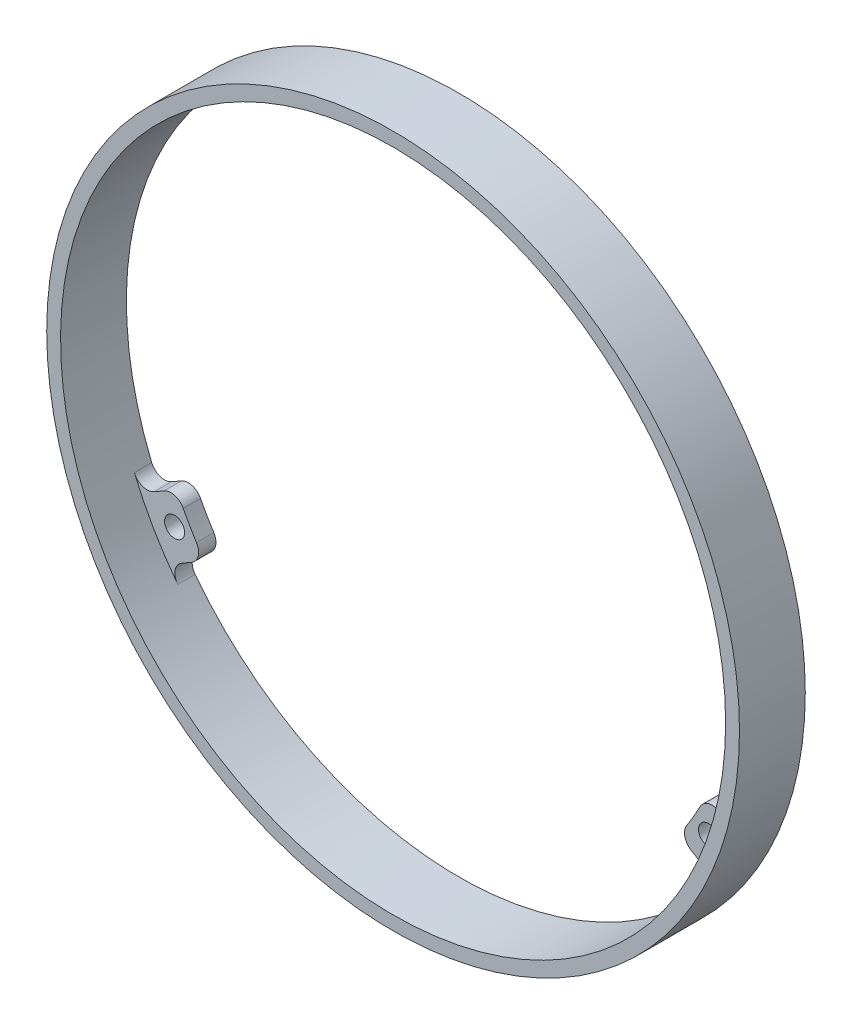
SolidWorks part; units mm, degrees
material "ABS"
ref_plane "Front Plane" through (0, 0, 0) normal (0, 0, 1) x (1, 0, 0)
ref_plane "Top Plane" through (0, 0, 0) normal (0, 1, 0) x (1, 0, 0)
ref_plane "Right Plane" through (0, 0, 0) normal (1, 0, 0) x (0, 0, -1)
sketch "Sketch1" plane through (0, 0, 0) normal (0, 0, 1) x (1, 0, 0)
  circle A0 centre (0, 0) radius 50
  circle A1 centre (0, 0) radius 48
  dimension "D1" = 100
  dimension "D2" = 2
extrude "Extrude1" add sketch "Sketch1" along normal blind 9.5
sketch "Sketch2" plane through (0, 0, 0) normal (0, 0, 1) x (1, 0, 0)
  line L0 (-4, 47.833) -> (-4, 41.8091)
  line L1 (0, 0) -> (0, 48) construction
  line L2 (4, 47.833) -> (4, 41.8091)
  arc A0 (4, 47.833) -> (-4, 47.833) centre (0, 0) ccw
  arc A1 (4, 41.8091) -> (-4, 41.8091) centre (0, 0) ccw
  circle A2 centre (0, 0) radius 48 construction
  dimension "D1" = 6
  dimension "D2" = 8
extrude "Extrude2" add sketch "Sketch2" along normal blind 2.5
sketch "Sketch3" plane through (0, 0, 2.5) normal (0, 0, 1) x (1, 0, 0)
  circle A0 centre (0, 44.5) radius 1.45
  arc A1 (4, 41.8091) -> (-4, 41.8091) centre (0, 0) ccw construction
  circle A2 centre (0, 0) radius 50 construction
  dimension "D1" = 2.9
  dimension "D2" = 44.5
extrude "Extrude3" cut sketch "Sketch3" against normal blind 2.5
fillet "Fillet1" radius 2 4 edges at (-4, 47.833, 1.25) (4, 47.833, 1.25) (4, 41.8091, 1.25) (-4, 41.8091, 1.25)
pattern_circular "CirPattern1" count 3 over 360 about axis through (0, 0, 0) along (0, 0, 1) of "Extrude2", "Extrude3", "Fillet1"
